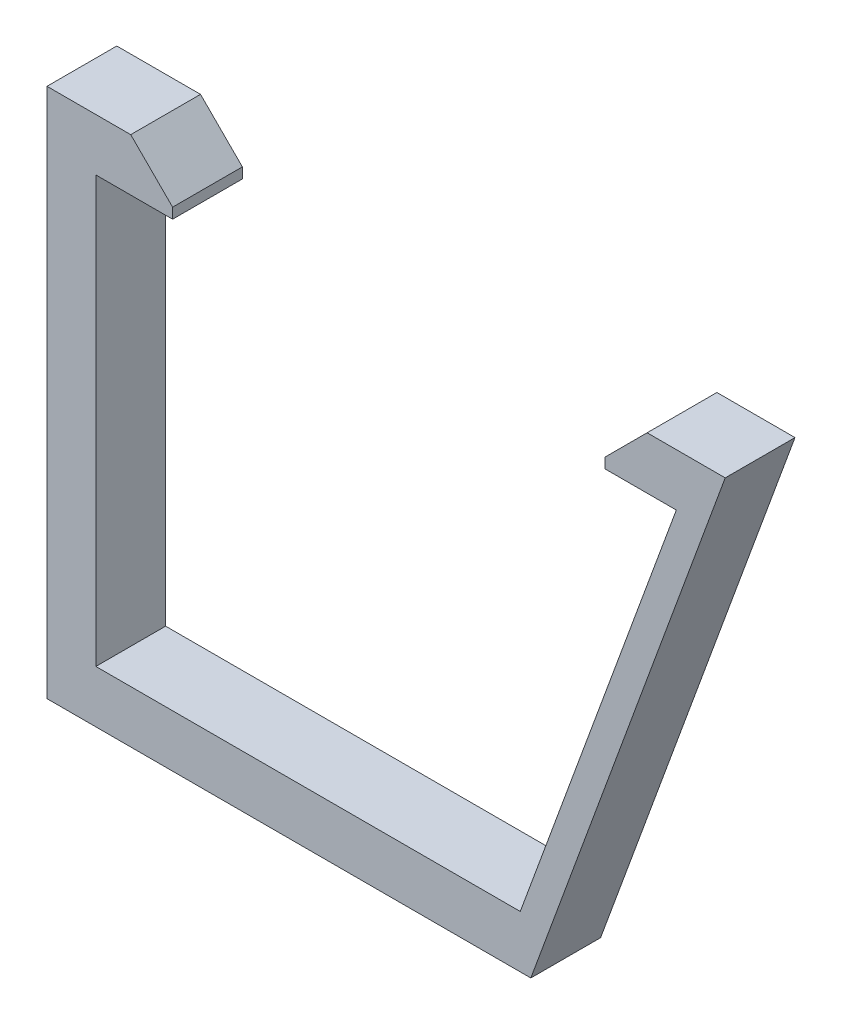
SolidWorks part; units mm, degrees
ref_plane "Front Plane" through (0, 0, 0) normal (0, 0, 1) x (1, 0, 0)
ref_plane "Top Plane" through (0, 0, 0) normal (0, 1, 0) x (1, 0, 0)
ref_plane "Right Plane" through (0, 0, 0) normal (1, 0, 0) x (0, 0, -1)
sketch "Sketch1" plane through (0, 0, 0) normal (0, 0, 1) x (1, 0, 0)
  line L0 (-315, 0) -> (315, 0)
  line L1 (-285.1688, 41.9) -> (-262.5188, 41.9)
  line L2 (-285.1688, 41.9) -> (-285.1688, 21.6)
  line L3 (-285.1688, 21.6) -> (-262.5188, 21.6)
  line L4 (-262.5188, 41.9) -> (-262.5188, 21.6)
  line L5 (262.5187, 41.9) -> (285.1687, 41.9)
  line L6 (262.5187, 41.9) -> (262.5187, 21.6)
  line L7 (262.5187, 21.6) -> (285.1687, 21.6)
  line L8 (285.1687, 41.9) -> (285.1687, 21.6)
  line L9 (-170.8687, 160.7) -> (-148.2188, 160.7)
  line L10 (-170.8687, 160.7) -> (-170.8687, 140.4)
  line L11 (-170.8687, 140.4) -> (-148.2188, 140.4)
  line L12 (-148.2188, 160.7) -> (-148.2188, 140.4)
  line L13 (148.2188, 160.7) -> (170.8688, 160.7)
  line L14 (148.2188, 160.7) -> (148.2188, 140.4)
  line L15 (148.2188, 140.4) -> (170.8688, 140.4)
  line L16 (170.8688, 160.7) -> (170.8688, 140.4)
  line L17 (-273.8438, 31.75) -> (273.8438, 31.75)
  line L18 (-159.5437, 150.55) -> (159.5437, 150.55)
  line L19 (315, 0) -> (315, 30.6)
  line L20 (-248.5188, 79.7) -> (-214.0187, 79.7)
  line L21 (-248.5188, 79.7) -> (-248.5188, 44.9)
  line L22 (-248.5188, 44.9) -> (-214.0187, 44.9)
  line L23 (-214.0187, 79.7) -> (-214.0187, 44.9)
  line L24 (-189.0187, 88.6) -> (-129.3687, 88.6)
  line L25 (-189.0187, 88.6) -> (-189.0187, 48.9)
  line L26 (-189.0187, 48.9) -> (-129.3687, 48.9)
  line L27 (-129.3687, 88.6) -> (-129.3687, 48.9)
  line L28 (-8.5687, 81.6) -> (61.1313, 81.6)
  line L29 (-8.5687, 81.6) -> (-8.5687, 46.9)
  line L30 (-8.5687, 46.9) -> (61.1313, 46.9)
  line L31 (61.1313, 81.6) -> (61.1313, 46.9)
  line L32 (315, 30.6) -> (254, 197)
  line L33 (254, 197) -> (-254, 197)
  line L34 (-254, 197) -> (-315, 30.6)
  line L35 (-315, 30.6) -> (-315, 0)
  line L36 (-315, 4.4515) -> (-244.4143, 197)
  circle A0 centre (-273.8438, 31.75) radius 2.05
  circle A1 centre (273.8438, 31.75) radius 2.05
  circle A2 centre (-159.5437, 150.55) radius 2.05
  circle A3 centre (159.5437, 150.55) radius 2.05
  circle A4 centre (-195.5187, 59.9) radius 2.05
  point P6 (0, 0)
  point P7 (-273.8438, 41.9)
  point P9 (-262.5187, 31.75)
  point P18 (273.8438, 41.9)
  point P19 (285.1688, 31.75)
  point P26 (-159.5437, 160.7)
  point P27 (-148.2188, 150.55)
  point P34 (159.5437, 160.7)
  point P35 (170.8687, 150.55)
  point P36 (0, 31.75)
  point P37 (0, 150.55)
  point P57 (0, 197)
  dimension "D3" = 4.1
  dimension "D7" = 4.1
  dimension "D10" = 4.1
  dimension "D13" = 4.1
  dimension "D18" = 4.1
  dimension "D1" = 22.65
  dimension "D2" = 20.3
  dimension "D4" = 630
  dimension "D5" = 22.65
  dimension "D6" = 20.3
  dimension "D8" = 22.65
  dimension "D9" = 20.3
  dimension "D11" = 22.65
  dimension "D12" = 20.3
  dimension "D14" = 547.6875
  dimension "D15" = 31.75
  dimension "D16" = 98.5
  dimension "D17" = 319.0875
  dimension "D19" = 6.5
  dimension "D20" = 69.7
  dimension "D21" = 34.7
  dimension "D22" = 59.65
  dimension "D23" = 39.7
  dimension "D24" = 34.5
  dimension "D25" = 34.8
  dimension "D26" = 14
  dimension "D27" = 3
  dimension "D28" = 25
  dimension "D29" = 4
  dimension "D30" = 11
  dimension "D31" = 120.8
  dimension "D32" = 2
  dimension "D33" = 30.6
  dimension "D34" = 508
  dimension "D35" = 36.3
  dimension "D36" = 197
  dimension "D37" = 9
sketch "Sketch2" plane through (0, 0, 0) normal (0, 0, 1) x (1, 0, 0)
  line L0 (-315, 0) -> (315, 0) construction
  line L1 (-375, 104) -> (375, 104)
  line L2 (-375, 104) -> (-375, 74)
  line L3 (-375, 74) -> (375, 74)
  line L4 (375, 104) -> (375, 74)
  line L6 (-315, 30.6) -> (-315, 0) construction
  line L7 (315, 0) -> (315, 30.6) construction
  dimension "D1" = 74
  dimension "D2" = 30
  dimension "D3" = 60
  dimension "D4" = 60
sketch "Sketch5" plane through (-8.3611, 207.407, 0) normal (0, 0, 1) x (0.7071, 0.7071, 0)
  line L1 (-321.6588, 154.019) -> (-101.6588, 154.019)
  line L2 (-321.6588, 154.019) -> (-321.6588, -65.981)
  line L3 (-321.6588, -65.981) -> (-101.6588, -65.981)
  line L4 (-101.6588, 154.019) -> (-101.6588, -65.981)
  dimension "D1" = 220
  dimension "D2" = 220
sketch "Sketch3" plane through (0, 0, 0) normal (0, 0, 1) x (1, 0, 0)
  line L0 (-148.2188, 160.7) -> (-148.2188, 140.4) construction
  line L1 (-288.1688, 18.6) -> (-145.2188, 18.6)
  line L2 (-288.1688, 18.6) -> (-288.1688, 163.7)
  line L3 (-288.1688, 163.7) -> (-145.2188, 163.7)
  line L4 (-145.2188, 18.6) -> (-145.2188, 163.7)
  line L5 (-170.8687, 160.7) -> (-148.2188, 160.7) construction
  line L6 (-285.1688, 21.6) -> (-262.5188, 21.6) construction
  line L7 (-285.1688, 41.9) -> (-285.1688, 21.6) construction
  line L8 (-288.1688, 18.6) -> (-289.5045, 74)
  line L9 (-315, 4.4515) -> (-244.4143, 197) construction
  line L10 (-375, 74) -> (375, 74) construction
  line L11 (-289.5045, 74) -> (-256.6217, 163.7)
  line L12 (-173.8687, 163.7) -> (-206.6045, 107)
  line L13 (-285.1688, 21.6) -> (-262.5188, 21.6)
  line L14 (-285.1688, 21.6) -> (-285.1688, 41.9)
  line L15 (-285.1688, 41.9) -> (-262.5188, 41.9)
  line L16 (-262.5188, 21.6) -> (-262.5188, 41.9)
  line L17 (-148.2188, 160.7) -> (-170.8687, 160.7)
  line L18 (-148.2188, 160.7) -> (-148.2188, 140.4)
  line L19 (-148.2188, 140.4) -> (-170.8687, 140.4)
  line L20 (-170.8687, 160.7) -> (-170.8687, 140.4)
  line L21 (-206.6045, 107) -> (-277.4071, 107)
  line L22 (-375, 104) -> (375, 104) construction
  line L23 (-259.5188, 18.6) -> (-259.5188, 71)
  line L24 (-259.5188, 71) -> (-145.2188, 71)
  line L25 (-259.5188, 71) -> (-289.4321, 71)
  line L26 (-206.6045, 107) -> (-145.2188, 107)
  circle A0 centre (-159.5437, 150.55) radius 2.05
  circle A1 centre (-273.8438, 31.75) radius 2.05
  dimension "D1" = 3
  dimension "D2" = 3
  dimension "D3" = 3
  dimension "D4" = 3
  dimension "D5" = 3
  dimension "D6" = 120
  dimension "D7" = 3
  dimension "D8" = 3
  dimension "D9" = 3
sketch "Sketch6" plane through (0, 0, 0) normal (0, 0, 1) x (1, 0, 0)
  line L0 (-375, 104) -> (375, 104) construction
  line L1 (-69.0901, 104) -> (-299.0901, 104)
  line L2 (-69.0901, 104) -> (-69.0901, 74)
  line L3 (-69.0901, 74) -> (-299.0901, 74)
  line L4 (-299.0901, 104) -> (-299.0901, 74)
  line L5 (-375, 74) -> (375, 74) construction
  line L6 (-254, 197) -> (-315, 30.6) construction
  line L9 (-299.0901, 74) -> (-310.0901, 74)
  line L10 (-299.0901, 74) -> (-299.0901, 104)
  line L11 (-299.0901, 104) -> (-310.0901, 104)
  line L12 (-310.0901, 74) -> (-310.0901, 104)
  dimension "D1" = 230
  dimension "D2" = 11
sketch "Sketch7" plane through (0, 0, 0) normal (0, 0, 1) x (1, 0, 0)
  line L0 (-284.4961, 108) -> (-298.4263, 70)
  line L1 (-375, 104) -> (375, 104) construction
  line L2 (-375, 74) -> (375, 74) construction
  line L3 (-254, 197) -> (-315, 30.6) construction
  line L4 (-329.0925, 70) -> (-298.4263, 70)
  line L5 (-284.4961, 108) -> (-329.0925, 108)
  line L6 (-288.0925, 104) -> (-288.0925, 108)
  line L7 (-299.0901, 74) -> (-288.0925, 104)
  line L8 (-329.0925, 70) -> (-333.0925, 70)
  line L9 (-329.0925, 70) -> (-329.0925, 108)
  line L10 (-329.0925, 108) -> (-333.0925, 108)
  line L11 (-333.0925, 70) -> (-333.0925, 108)
  line L12 (-333.0925, 79) -> (-329.0925, 79)
  line L13 (-333.0925, 79) -> (-333.0925, 99)
  line L14 (-333.0925, 99) -> (-329.0925, 99)
  line L15 (-329.0925, 79) -> (-329.0925, 99)
  line L16 (-299.0901, 74) -> (-329.0925, 74)
  line L17 (-329.0925, 74) -> (-329.0925, 79)
  line L18 (-329.0925, 99) -> (-329.0925, 104)
  line L19 (-329.0925, 104) -> (-288.0925, 104)
  line L20 (-299.0901, 74) -> (-300.5565, 70)
  line L21 (-288.0925, 104) -> (-286.6262, 108)
  line L22 (-299.1818, 104.25) -> (-288.0009, 104.25)
  line L23 (-324.0925, 104) -> (-293.0925, 104)
  line L24 (-324.0925, 104) -> (-324.0925, 108)
  line L25 (-324.0925, 108) -> (-293.0925, 108)
  line L26 (-293.0925, 104) -> (-293.0925, 108)
  line L27 (-329.5925, 104.25) -> (-299.1818, 104.25)
  line L28 (-329.5925, 104.25) -> (-329.5925, 73.75)
  line L29 (-329.5925, 73.75) -> (-299.1818, 73.75)
  line L30 (-299.1818, 104.25) -> (-299.1818, 73.75)
  line L31 (-288.0009, 104.25) -> (-299.1818, 73.75)
  point P19 (-333.0925, 89)
  point P20 (-333.0925, 89)
  point P21 (-329.0925, 89)
  point P22 (-329.0925, 89)
  dimension "D1" = 2
  dimension "D2" = 4
  dimension "D3" = 4
  dimension "D4" = 41
  dimension "D5" = 5
  dimension "D6" = 4
  dimension "D7" = 20
  dimension "D8" = 5
  dimension "D9" = 0.25
  dimension "D10" = 0.25
  dimension "D11" = 0.5
extrude "Boss-Extrude3" add sketch "Sketch7" along normal blind 5 contours L12 L11 L8 L9 | L20 L16 L9 L4 | L21 L7 L20 L4 L0 L5 | L26 L19 L6 L5 | L6 L21 L5 | L19 L24 L5 L9 | L11 L14 L9 L10 | L14 L11 L12 L9
chamfer "Chamfer3" distance 3 angle 45 2 edges at (-293.0925, 108, 2.5) (-324.0925, 108, 2.5)
equation "\"D1@Chamfer2\"=5-1.8"
